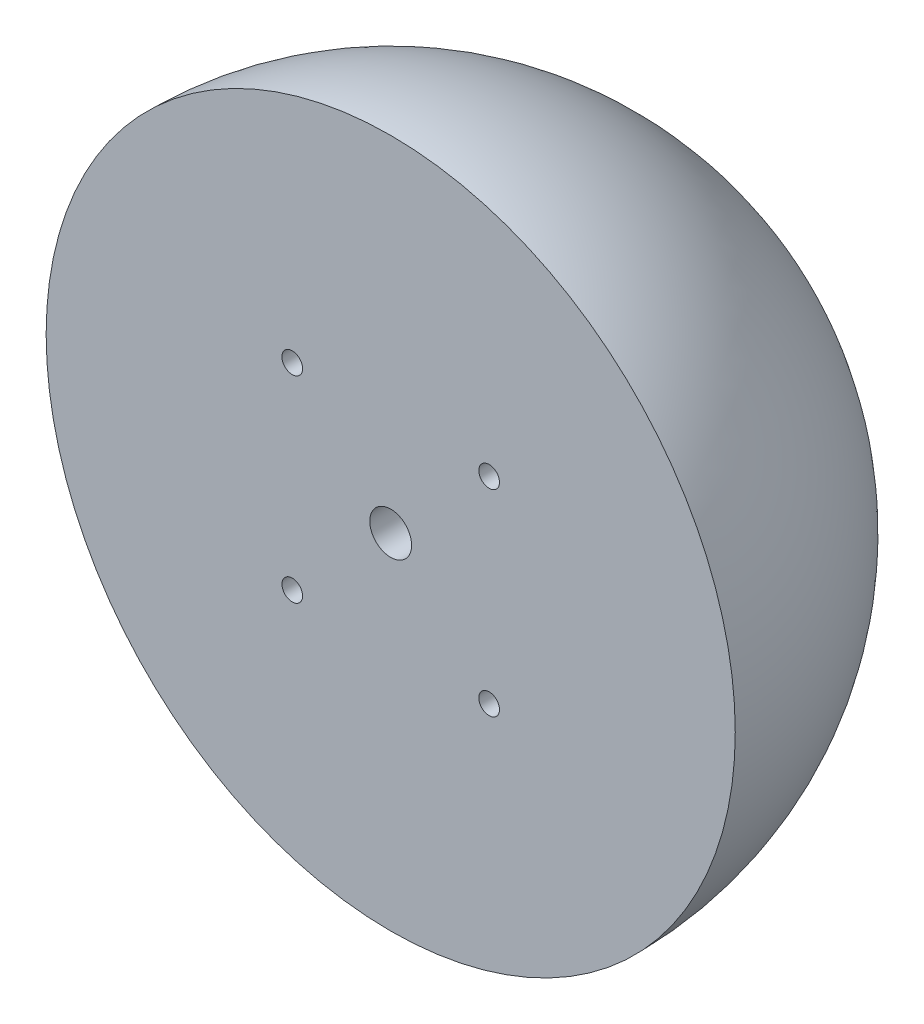
SolidWorks part; units mm, degrees
material "AISI 321 Annealed Stainless Steel (SS)"
ref_plane "Front Plane" through (0, 0, 0) normal (0, 0, 1) x (1, 0, 0)
ref_plane "Top Plane" through (0, 0, 0) normal (0, 1, 0) x (1, 0, 0)
ref_plane "Right Plane" through (0, 0, 0) normal (1, 0, 0) x (0, 0, -1)
sketch "Sketch2" plane through (0, 0, 0) normal (0, 1, 0) x (1, 0, 0)
  line L0 (0, 70) -> (0, 0)
  line L1 (0, 0) -> (70, 0)
  arc A0 (70, 0) -> (0, 70) centre (0, 0) ccw
  dimension "D1" = 70
revolve "Revolve1" add sketch "Sketch2" angle 360 about L0
sketch "Sketch3" plane through (0, 0, 0) normal (0, 0, 1) x (1, 0, 0)
  line L0 (0, 76.4704) -> (0, -76.3825) construction
  line L1 (-84.6195, 0.044) -> (77.8151, 0.044) construction
  line L3 (-20, -20) -> (20, -20) construction
  line L4 (-20, -20) -> (-20, 20) construction
  line L5 (-20, 20) -> (20, 20) construction
  line L6 (20, -20) -> (20, 20) construction
  line L7 (-20, -20) -> (20, 20) construction
  line L8 (-20, 20) -> (20, -20) construction
  point P5 (0, 0)
  dimension "D1" = 40
hole_wizard "M10 Tapped Hole1" positions "Sketch4" profile "Sketch5" tap size "M10" standard "ISO"
sketch "Sketch4" plane through (0, 0, 0) normal (0, 0, 1) x (1, 0, 0)
  line L0 (-20, 20) -> (20, -20) construction
  point P0 (0, 0)
  point P4 (0, 0)
sketch "Sketch5" plane through (0, 0, 0) normal (1, 0, 0) x (0, -1, 0)
  line L0 (0, 0) -> (0, 32.5537)
  line L1 (0, 32.5537) -> (4.25, 30)
  line L2 (4.25, 30) -> (4.25, 0)
  line L5 (4.25, 0) -> (0, 0)
  line L10 (0, 32.5537) -> (-4.25, 30) construction
  line L11 (0, -6.35) -> (0, 107.95) construction
  dimension "Tap Drill Dia." = 8.5
  dimension "Tap Drill Depth" = 30
  dimension "Drill Angle" = 118
cosmetic thread "Hole Thread1" parameters "D1"=20, "D2"=10
cosmetic thread "Hole Thread6" parameters "D1"=20, "D2"=10
hole_wizard "M5 Tapped Hole1" positions "Sketch6" profile "Sketch7" tap size "M5" standard "ISO"
sketch "Sketch6" plane through (0, 0, 0) normal (0, 0, 1) x (1, 0, 0)
  point P0 (-20, 20)
  point P3 (20, 20)
  point P6 (20, -20)
  point P9 (-20, -20)
sketch "Sketch7" plane through (-20, 20, 0) normal (1, 0, 0) x (0, -1, 0)
  line L0 (0, 0) -> (0, 21.2618)
  line L1 (0, 21.2618) -> (2.1, 20)
  line L2 (2.1, 20) -> (2.1, 0)
  line L5 (2.1, 0) -> (0, 0)
  line L10 (0, 21.2618) -> (-2.1, 20) construction
  line L11 (0, -6.35) -> (0, 107.95) construction
  dimension "Tap Drill Dia." = 4.2
  dimension "Tap Drill Depth" = 20
  dimension "Drill Angle" = 118
cosmetic thread "Hole Thread2" parameters "D1"=18.5, "D2"=5
cosmetic thread "Hole Thread3" parameters "D1"=18.5, "D2"=5
cosmetic thread "Hole Thread4" parameters "D1"=18.5, "D2"=5
cosmetic thread "Hole Thread5" parameters "D1"=18.5, "D2"=5
